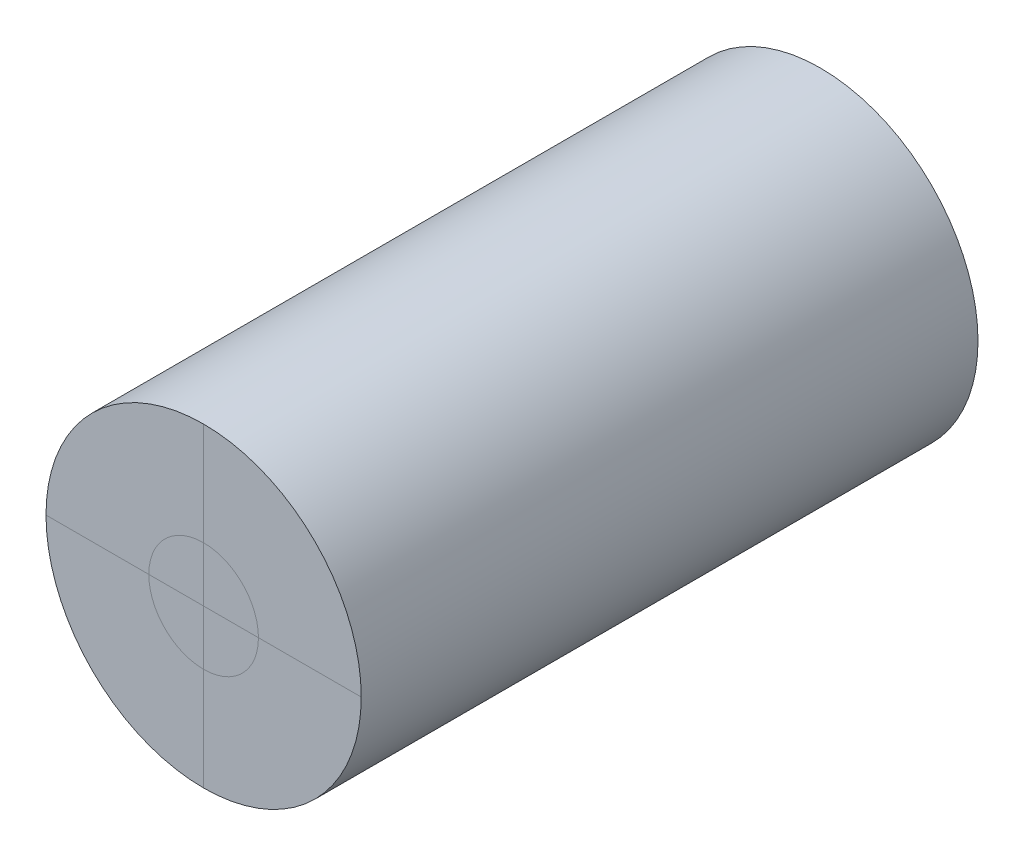
SolidWorks part; units mm, degrees
ref_plane "Front Plane" through (0, 0, 0) normal (0, 0, 1) x (1, 0, 0)
ref_plane "Top Plane" through (0, 0, 0) normal (0, 1, 0) x (1, 0, 0)
ref_plane "Right Plane" through (0, 0, 0) normal (1, 0, 0) x (0, 0, -1)
sketch "Sketch1" plane through (0, 0, 0) normal (0, 0, 1) x (1, 0, 0)
  circle A0 centre (0, 0) radius 14.605
  dimension "D1" = 29.21
extrude "Boss-Extrude1" add sketch "Sketch1" along normal blind 57.15
sketch "Sketch2" plane through (0, 0, 57.15) normal (0, 0, 1) x (1, 0, 0)
  line L0 (-14.605, 0) -> (14.605, 0)
  line L2 (0, 14.605) -> (0, -14.605)
  circle A0 centre (0, 0) radius 14.605 construction
  circle A1 centre (0, 0) radius 5.08
  dimension "D1" = 10.16
split line "Split Line1"
